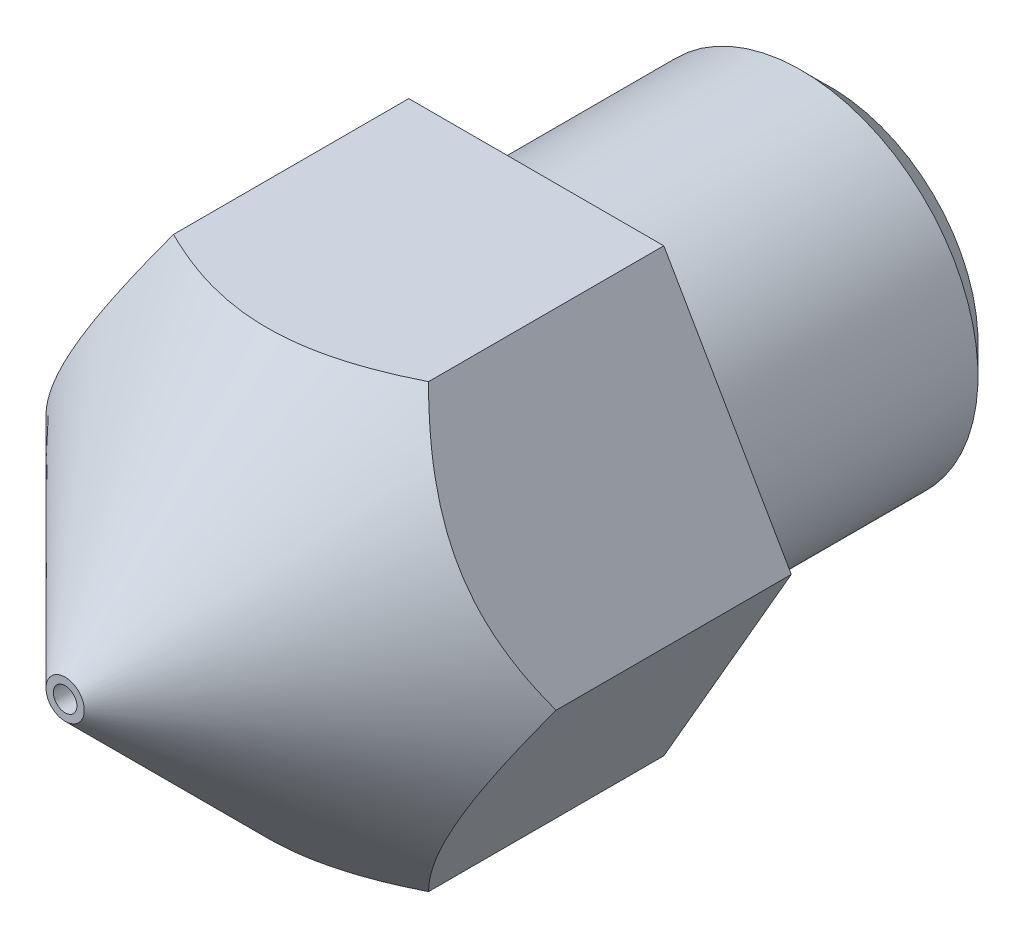
SolidWorks part; units mm, degrees
material "黄铜"
ref_plane "Front Plane" through (0, 0, 0) normal (0, 0, 1) x (1, 0, 0)
ref_plane "Top Plane" through (0, 0, 0) normal (0, 1, 0) x (1, 0, 0)
ref_plane "Right Plane" through (0, 0, 0) normal (1, 0, 0) x (0, 0, -1)
sketch "Sketch1" plane through (0, 0, 0) normal (0, 1, 0) x (1, 0, 0)
  line L0 (0, 0) -> (0, -50000) construction
  line L1 (1.55, 0) -> (0, 0) construction
  line L2 (1.55, 0) -> (3, 0)
  line L3 (0.325, -13) -> (8.325, -5)
  line L4 (1.55, 0) -> (1.55, -1)
  line L5 (0.2, -13) -> (0.2, -12.5)
  line L6 (1.55, -1) -> (1, -1)
  line L7 (1, -1) -> (1, -10)
  line L9 (1, -10) -> (1, -10.9)
  line L10 (1, -10.9) -> (0.2, -12.5)
  line L14 (3, 0) -> (3, -5)
  line L23 (3, -5) -> (8.325, -5)
  line L24 (0.2, -13) -> (0.325, -13)
  dimension "D2" = 3
  dimension "D3" = 1.55
  dimension "D4" = 0.125
  dimension "D5" = 0.5
  dimension "D6" = 13
  dimension "D7" = 5
  dimension "D8" = 0.4
  dimension "D9" = 1.6
  dimension "D10" = 1
  dimension "  " = 45
  dimension "D12" = 1
  dimension "D13" = 9
ref_axis "Axis1" through (0, 0, 0) along (0, 0, 1)
revolve "Revolve1" add sketch "Sketch1" angle 360 about axis through (0, 0, 0) along (0, 0, 1)
cosmetic thread "装饰螺纹线1" [suppressed] parameters "D2"=4.917
sketch "Sketch2" plane through (0, 0, 5) normal (0, 0, -1) x (-1, 0, 0)
  line L0 (0, 0) -> (0, 50000) construction
  line L1 (0, 0) -> (50000, 0) construction
  line L5 (0, 0) -> (43301.2702, 25000) construction
  line L6 (0, 0) -> (43062.4912, -24862.1409) construction
  line L11 (-4.3301, 0) -> (-2.1651, -3.75)
  line L12 (-2.1651, -3.75) -> (2.1651, -3.75)
  line L13 (2.1651, -3.75) -> (4.3301, 0)
  line L14 (4.3301, 0) -> (2.1651, 3.75)
  line L15 (2.1651, 3.75) -> (-2.1651, 3.75)
  line L16 (-2.1651, 3.75) -> (-4.3301, 0)
  circle A0 centre (0, 0) radius 3.75 construction
  circle A1 centre (0, 0) radius 8.325
  circle A3 centre (0, 0) radius 8.325 construction
  dimension "D1" = 60
  dimension "D2" = 30
  dimension "D3" = 7.5
extrude "Cut-Extrude2" cut sketch "Sketch2" against normal blind 10
chamfer "Chamfer1" distance 0.5 angle 45 1 edges at (-3, 0, 0)
